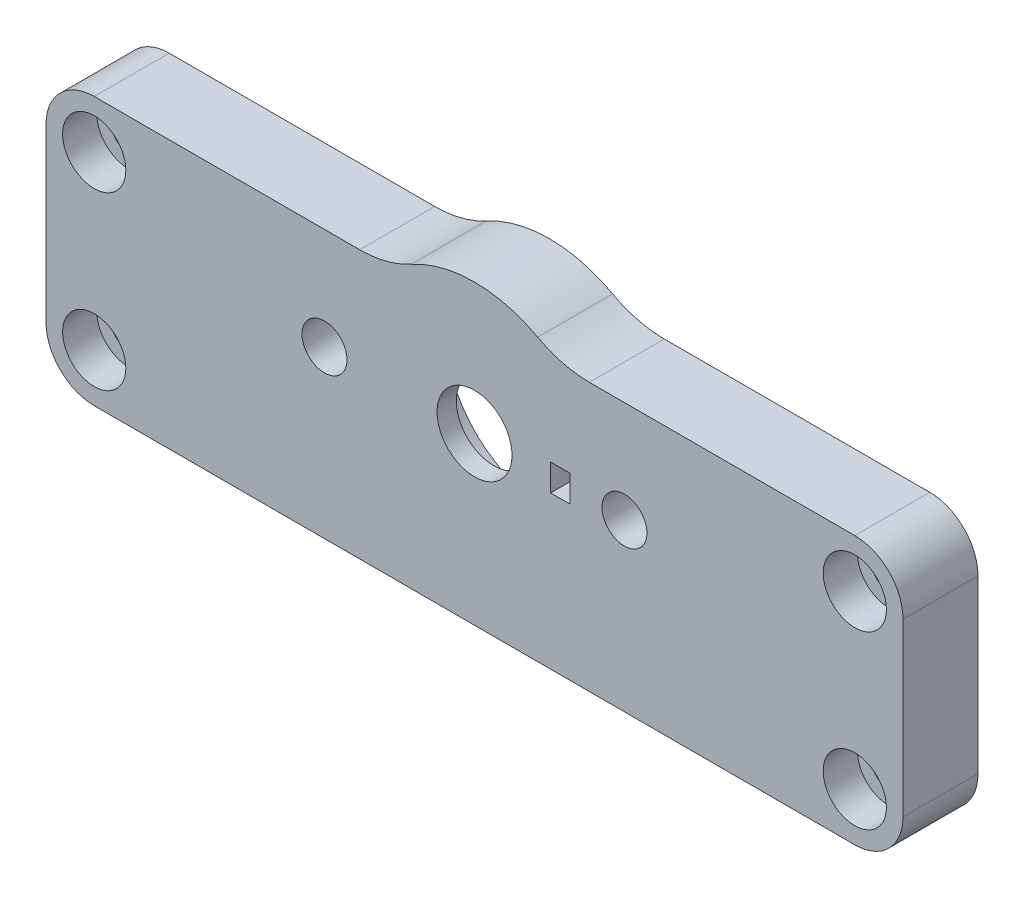
SolidWorks part; units mm, degrees
ref_plane "Front Plane" through (0, 0, 0) normal (0, 0, 1) x (1, 0, 0)
ref_plane "Top Plane" through (0, 0, 0) normal (0, 1, 0) x (1, 0, 0)
ref_plane "Right Plane" through (0, 0, 0) normal (1, 0, 0) x (0, 0, -1)
sketch "Sketch1" plane through (0, 0, 0) normal (0, 0, 1) x (1, 0, 0)
  line L0 (0, 0) -> (-40, 0) construction
  line L2 (-35.5, 9.5) -> (-7.7339, 9.5)
  line L3 (0, 0) -> (0, 12.25) construction
  line L6 (35.5, -15.5) -> (-35.5, -15.5)
  line L7 (-40, -11) -> (-40, 5)
  line L8 (35.5, 9.5) -> (7.7339, 9.5)
  line L10 (40, -11) -> (40, 5)
  circle A0 centre (0, 0) radius 9.75
  arc A1 (-7.7339, 9.5) -> (7.7339, 9.5) centre (0, 0) cw
  arc A16 (-35.5, -15.5) -> (-40, -11) centre (-35.5, -11) cw
  arc A17 (-40, 5) -> (-35.5, 9.5) centre (-35.5, 5) cw
  circle A18 centre (-35.5, 5) radius 1.65
  circle A25 centre (35.5, 5) radius 1.65
  arc A26 (40, 5) -> (35.5, 9.5) centre (35.5, 5) ccw
  arc A27 (35.5, -15.5) -> (40, -11) centre (35.5, -11) ccw
  circle A29 centre (-35.5, -11) radius 1.65
  circle A31 centre (35.5, -11) radius 1.65
  dimension "D1" = 19.5
  dimension "D2" = 2.5
  dimension "D4" = 4.5
  dimension "D5" = 40
  dimension "D3" = 16
  dimension "D7" = 3.3
  dimension "D6" = 5
extrude "Boss-Extrude1" add sketch "Sketch1" along normal blind 7
fillet "Fillet1" radius 10 2 edges at (7.7339, 9.5, 3.5) (-7.7339, 9.5, 3.5)
sketch "Sketch2" plane through (0, 0, 7) normal (0, 0, 1) x (1, 0, 0)
  circle A0 centre (0, 0) radius 7.5
  circle A1 centre (0, 0) radius 9.75 construction
  circle A2 centre (0, 0) radius 9.75
  dimension "D1" = 15
extrude "Boss-Extrude2" add sketch "Sketch2" against normal blind 2
sketch "Sketch3" plane through (0, 0, 7) normal (0, 0, 1) x (1, 0, 0)
  circle A0 centre (0, 0) radius 3.5
  circle A1 centre (0, 0) radius 7.5
  circle A2 centre (0, 0) radius 7.5 construction
  dimension "D1" = 7
extrude "Boss-Extrude3" add sketch "Sketch3" against normal blind 1.8
sketch "Sketch4" plane through (0, 0, 7) normal (0, 0, 1) x (1, 0, 0)
  line L0 (0, 0) -> (8, 0) construction
  line L2 (7.1, -1.25) -> (8.9, -1.25)
  line L3 (7.1, -1.25) -> (7.1, 1.25)
  line L4 (7.1, 1.25) -> (8.9, 1.25)
  line L5 (8.9, -1.25) -> (8.9, 1.25)
  line L6 (7.1, -1.25) -> (8.9, 1.25) construction
  line L7 (7.1, 1.25) -> (8.9, -1.25) construction
  dimension "D1" = 1.8
  dimension "D2" = 2.5
  dimension "D3" = 8
extrude "Cut-Extrude1" cut sketch "Sketch4" against normal blind 2.5
sketch "Sketch5" plane through (0, 0, 7) normal (0, 0, 1) x (1, 0, 0)
  line L0 (0, 0) -> (0, 12.25) construction
  arc A0 (5.8993, 10.736) -> (-5.8993, 10.736) centre (0, 0) ccw construction
  circle A1 centre (-14, 0) radius 2.1
  circle A2 centre (14, 0) radius 2.1
  dimension "D1" = 4.2
  dimension "D2" = 14
extrude "Cut-Extrude2" cut sketch "Sketch5" against normal blind 3
sketch "Sketch6" plane through (0, 0, 7) normal (0, 0, 1) x (1, 0, 0)
  circle A0 centre (-35.5, 5) radius 2.95
  circle A1 centre (-35.5, -11) radius 2.95
  circle A2 centre (35.5, -11) radius 2.95
  circle A3 centre (35.5, 5) radius 2.95
  dimension "D1" = 5.9
extrude "Cut-Extrude3" cut sketch "Sketch6" against normal blind 3.2
